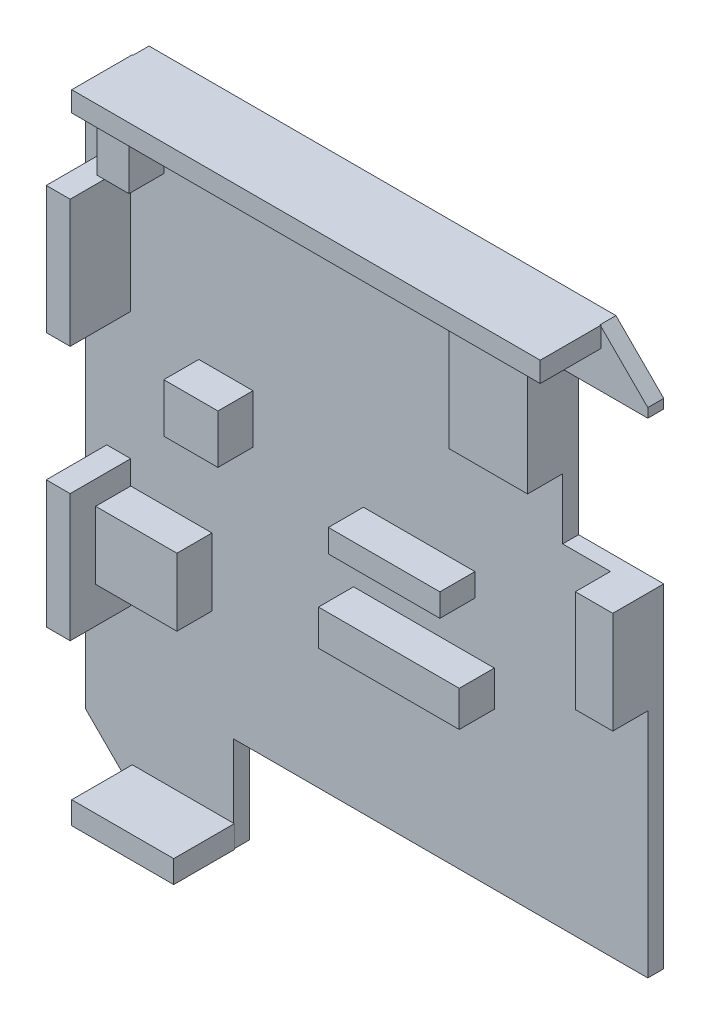
SolidWorks part; units mm, degrees
ref_plane "前视基准面" through (0, 0, 0) normal (0, 0, 1) x (1, 0, 0)
ref_plane "上视基准面" through (0, 0, 0) normal (0, 1, 0) x (1, 0, 0)
ref_plane "右视基准面" through (0, 0, 0) normal (1, 0, 0) x (0, 0, -1)
sketch "草图1" plane through (0, 0, 0) normal (0, 0, 1) x (1, 0, 0)
  line L0 (-17.75, 18) -> (-17.75, -18) construction
  line L1 (14.65, 20) -> (-14.65, 20)
  line L2 (17.65, 17) -> (17.65, 16.4206)
  line L3 (-8.35, -20) -> (-14.65, -20)
  line L4 (-17.65, 17) -> (-17.65, -17)
  line L5 (17.65, 20) -> (-17.65, -20) construction
  line L6 (17.65, -20) -> (-17.65, 20) construction
  line L7 (-14.65, 20) -> (-17.65, 17)
  line L8 (17.65, 17) -> (14.65, 20)
  line L10 (-14.65, -20) -> (-17.65, -17)
  line L11 (14.3059, 15.4206) -> (15.5211, 15.4206) construction
  line L12 (17.65, 16.4206) -> (12.3058, 16.4206)
  line L14 (17.65, 6.9197) -> (12.3058, 6.9197)
  line L15 (12.3058, 16.4206) -> (12.3058, 6.9197)
  line L16 (14.3059, 7.9197) -> (15.5211, 7.9197) construction
  line L17 (13.3058, 8.4697) -> (13.3058, 7.9197) construction
  line L18 (17.65, 6.9197) -> (17.65, -14)
  line L21 (-8.35, -20) -> (-8.35, -14)
  line L22 (-8.35, -14) -> (17.65, -14)
  point P0 (0, 0)
  dimension "D1" = 0.1
  dimension "D2" = 40
  dimension "D3" = 1
  dimension "D4" = 1
  dimension "D9" = 1
  dimension "D10" = 6
  dimension "D11" = 26
extrude "Base" add sketch "草图1" along normal blind 1
sketch "草图2" plane through (0, 0, 1) normal (0, 0, 1) x (1, 0, 0)
  line L0 (-14.6993, 15.5) -> (-14.6993, -15.5) construction
  line L1 (-14.6993, -3.489) -> (-9.6993, -3.489)
  line L2 (-14.6993, -3.489) -> (-14.6993, -7.73)
  line L3 (-14.6993, -7.73) -> (-9.6993, -7.73)
  line L4 (-9.6993, -3.489) -> (-9.6993, -7.73)
  line L5 (15.288, 18.4873) -> (-11.712, 18.4873) construction
  line L6 (-10.5257, 5.528) -> (-7.126, 5.528)
  line L7 (-10.5257, 5.528) -> (-10.5257, 2.459)
  line L8 (-10.5257, 2.459) -> (-7.126, 2.459)
  line L9 (-7.126, 5.528) -> (-7.126, 2.459)
  line L10 (-0.817, -1.973) -> (8.016, -1.973)
  line L11 (-0.817, -1.973) -> (-0.817, -4.2123)
  line L12 (-0.817, -4.2123) -> (8.016, -4.2123)
  line L13 (8.016, -1.973) -> (8.016, -4.2123)
  line L14 (-0.197, 2.6628) -> (6.803, 2.6628)
  line L15 (-0.197, 2.6628) -> (-0.197, 1.2225)
  line L16 (-0.197, 1.2225) -> (6.803, 1.2225)
  line L17 (6.803, 2.6628) -> (6.803, 1.2225)
  line L18 (17.65, 6.9197) -> (15.303, 6.9197)
  line L19 (17.65, 6.9197) -> (17.65, 0.517)
  line L20 (17.65, 0.517) -> (15.303, 0.517)
  line L21 (15.303, 6.9197) -> (15.303, 0.517)
  line L22 (7.3846, 18.4873) -> (12.3058, 18.4873)
  line L23 (7.3846, 18.4873) -> (7.3846, 10.732)
  line L24 (7.3846, 10.732) -> (12.3058, 10.732)
  line L25 (12.3058, 18.4873) -> (12.3058, 10.732)
  line L26 (12.3058, 6.9197) -> (12.3058, 16.4206) construction
  line L27 (-13.5123, -1.989) -> (-12.413, -1.989) construction
  line L28 (-14.6993, 14.5462) -> (-12.7065, 14.5462)
  line L29 (-14.6993, 14.5462) -> (-14.6993, 18.3169)
  line L30 (-14.6993, 18.3169) -> (-12.7065, 18.3169)
  line L31 (-12.7065, 14.5462) -> (-12.7065, 18.3169)
  line L32 (-12.4058, -9.23) -> (-13.5022, -9.23) construction
  line L33 (0.65, -4.8123) -> (0.85, -4.8123) construction
  line L34 (1.124, -1.373) -> (1.884, -1.373) construction
  line L35 (-1.817, 0.9093) -> (-1.817, -1.8413) construction
  line L36 (9.516, -6.183) -> (9.516, -4.483) construction
  line L37 (-0.888, 0.2225) -> (-0.128, 0.2225) construction
  line L38 (0.94, 3.6628) -> (0.33, 3.6628) construction
  line L39 (8.303, 2.24) -> (8.303, 2.67) construction
  line L40 (-12.0257, 4.2276) -> (-12.0257, 3.8277) construction
  line L41 (-7.295, 1.459) -> (-6.675, 1.459) construction
  line L42 (-8.0427, 7.028) -> (-6.9433, 7.028) construction
  line L43 (-5.626, 5.3172) -> (-5.626, 5.9428) construction
  line L44 (14.866, -0.983) -> (15.066, -0.983) construction
  line L45 (14.303, 4.78) -> (14.303, 5.21) construction
  line L46 (6.3846, 13.8782) -> (6.3846, 10.0819) construction
  line L47 (7.748, 9.732) -> (8.508, 9.732) construction
  line L48 (-13.6115, 13.5462) -> (-13.364, 13.5462) construction
  line L49 (-11.7065, 16.1774) -> (-11.7065, 16.9374) construction
  arc A0 (-11.712, 18.4873) -> (-14.6993, 15.5) centre (-11.712, 15.5) ccw construction
  point P74 (-13.4878, 13.5462)
  dimension "D1" = 5
  dimension "D2" = 1.5
  dimension "D3" = 1.5
  dimension "D4" = 0.6
  dimension "D5" = 0.6
  dimension "D6" = 1
  dimension "D7" = 1.5
  dimension "D8" = 1
  dimension "D9" = 1
  dimension "D10" = 1.5
  dimension "D11" = 7
  dimension "D12" = 1.5
  dimension "D13" = 1
  dimension "D14" = 1.5
  dimension "D15" = 1.5
  dimension "D16" = 1.5
  dimension "D17" = 1
  dimension "D18" = 1
  dimension "D19" = 1
  dimension "D20" = 1
  dimension "D21" = 1
extrude "Pillars" add sketch "草图2" along normal up to surface (2.2 mm away)
sketch "草图3" plane through (0, 0, 1) normal (0, 0, 1) x (1, 0, 0)
  line L4 (-14.7993, 14) -> (-16.2993, 14)
  line L5 (-14.7993, 6) -> (-14.7993, 14)
  line L6 (-16.2993, 6) -> (-14.7993, 6)
  line L7 (-16.2993, 14) -> (-16.2993, 6)
  line L8 (-14.7993, 14) -> (-16.2993, 14)
  line L9 (-14.7993, 6) -> (-14.7993, 14)
  line L10 (-16.2993, 6) -> (-14.7993, 6)
  line L11 (-16.2993, 14) -> (-16.2993, 6)
  line L12 (14.7, 20) -> (-14.7, 20)
  line L13 (14.7, 18.7314) -> (14.7, 20)
  line L14 (-14.7, 18.7314) -> (14.7, 18.7314)
  line L15 (-14.7, 20) -> (-14.7, 18.7314)
  line L16 (14.7, 20) -> (-14.7, 20)
  line L17 (14.7, 18.7314) -> (14.7, 20)
  line L18 (-14.7, 18.7314) -> (14.7, 18.7314)
  line L19 (-14.7, 20) -> (-14.7, 18.7314)
  line L20 (-14.7, -20) -> (-8.3, -20)
  line L21 (-14.7, -18.5873) -> (-14.7, -20)
  line L22 (-8.3, -18.5873) -> (-14.7, -18.5873)
  line L23 (-8.3, -20) -> (-8.3, -18.5873)
  line L24 (-14.7, -20) -> (-8.3, -20)
  line L25 (-14.7, -18.5873) -> (-14.7, -20)
  line L26 (-8.3, -18.5873) -> (-14.7, -18.5873)
  line L27 (-8.3, -20) -> (-8.3, -18.5873)
  line L28 (-14.7993, -2) -> (-16.2993, -2)
  line L29 (-16.2993, -2) -> (-16.2993, -10)
  line L30 (-16.2993, -10) -> (-14.7993, -10)
  line L31 (-14.7993, -10) -> (-14.7993, -2)
  line L32 (-14.7993, -2) -> (-16.2993, -2)
  line L33 (-16.2993, -2) -> (-16.2993, -10)
  line L34 (-16.2993, -10) -> (-14.7993, -10)
  line L35 (-14.7993, -10) -> (-14.7993, -2)
  dimension "D1" = 0
  dimension "D2" = 0
  dimension "D3" = 0
  dimension "D4" = 0
extrude "Enclosure" add sketch "草图3" along normal up to surface (3.8001 mm away)
sketch "草图5" plane through (0, 0, 3.2) normal (0, 0, 1) x (1, 0, 0)
  line L0 (-14.7, 18.7314) -> (14.7, 18.7314) construction
  line L1 (-14.6993, 18.3169) -> (-12.7065, 18.3169)
  line L2 (-14.6993, 18.3169) -> (-14.6993, 18.7314)
  line L3 (-14.6993, 18.7314) -> (-12.7065, 18.7314)
  line L4 (-12.7065, 18.3169) -> (-12.7065, 18.7314)
  line L5 (-14.7, 18.7314) -> (14.7, 18.7314) construction
  line L6 (7.3846, 18.4873) -> (12.3058, 18.4873)
  line L7 (7.3846, 18.4873) -> (7.3846, 18.7314)
  line L8 (7.3846, 18.7314) -> (12.3058, 18.7314)
  line L9 (12.3058, 18.4873) -> (12.3058, 18.7314)
  line L10 (-14.7993, -10) -> (-14.7993, -2) construction
  line L15 (-14.6993, -7.73) -> (-14.7993, -7.73)
  line L16 (-14.6993, -7.73) -> (-14.6993, -3.489)
  line L17 (-14.6993, -3.489) -> (-14.7993, -3.489)
  line L18 (-14.7993, -7.73) -> (-14.7993, -3.489)
extrude "Padding" add sketch "草图5" against normal up to next
